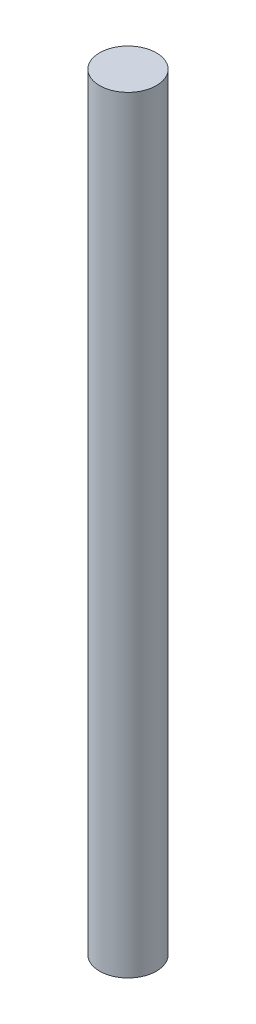
SolidWorks part; units mm, degrees
material "AISI 1045 Aço, trefilado"
ref_plane "Plano frontal" through (0, 0, 0) normal (0, 0, 1) x (1, 0, 0)
ref_plane "Plano superior" through (0, 0, 0) normal (0, 1, 0) x (1, 0, 0)
ref_plane "Plano direito" through (0, 0, 0) normal (1, 0, 0) x (0, 0, -1)
sketch "Esboço1" plane through (0, 0, 0) normal (0, 1, 0) x (1, 0, 0)
  circle A0 centre (0, 0) radius 5
  dimension "D1" = 10
extrude "Ressalto-extrusão1" add sketch "Esboço1" along normal blind 135
